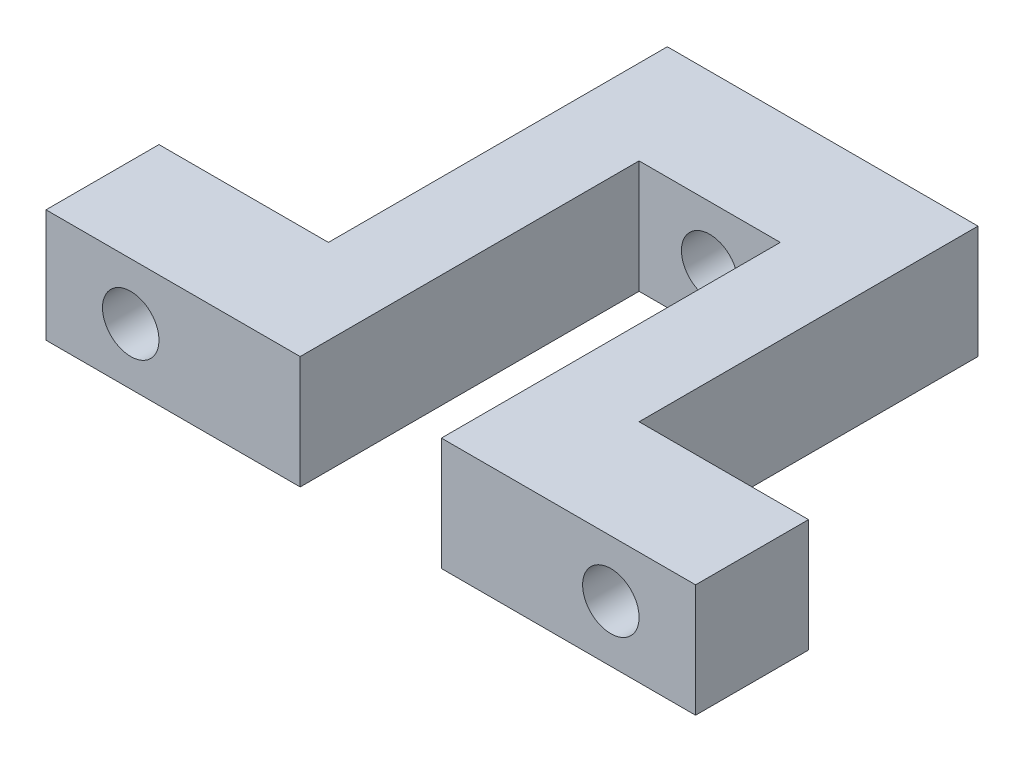
SolidWorks part; units mm, degrees
material "Copper"
ref_plane "Front Plane" through (0, 0, 0) normal (0, 0, 1) x (1, 0, 0)
ref_plane "Top Plane" through (0, 0, 0) normal (0, 1, 0) x (1, 0, 0)
ref_plane "Right Plane" through (0, 0, 0) normal (1, 0, 0) x (0, 0, -1)
sketch "Sketch1" plane through (0, 0, 0) normal (0, 1, 0) x (1, 0, 0)
  line L0 (-70, -38.8484) -> (-70, -18.8484)
  line L1 (-70, -18.8484) -> (-40, -18.8484)
  line L2 (-40, -18.8484) -> (-40, 41.1516)
  line L3 (-40, 41.1516) -> (15, 41.1516)
  line L4 (15, 41.1516) -> (15, -18.8484)
  line L5 (15, -18.8484) -> (45, -18.8484)
  line L6 (45, -18.8484) -> (45, -38.8484)
  line L7 (45, -38.8484) -> (0, -38.8484)
  line L8 (0, -38.8484) -> (0, 21.1516)
  line L9 (0, 21.1516) -> (-25, 21.1516)
  line L10 (-25, 21.1516) -> (-25, -38.8484)
  line L11 (-25, -38.8484) -> (-70, -38.8484)
  dimension "D1" = 20
  dimension "D2" = 30
  dimension "D3" = 60
  dimension "D4" = 55
  dimension "D5" = 60
  dimension "D6" = 30
  dimension "D7" = 20
  dimension "D8" = 45
  dimension "D9" = 45
  dimension "D10" = 60
extrude "Boss-Extrude1" add sketch "Sketch1" along normal blind 20
ref_plane "Plane1" through (0, 0, -41.1516) normal (0, 0, -1) x (-1, 0, 0)
sketch "Sketch2" plane through (0, 0, -41.1516) normal (0, 0, -1) x (-1, 0, 0)
  point P6 (12.5, 10)
hole_wizard "M10x1.0 Tapped Hole1" positions "3DSketch1" profile "Sketch3" tap size "M10x1.0" standard "ANSI Metric"
sketch3d "3DSketch1"
  point P0 (-12.5, 10, -41.1516)
sketch "Sketch3" plane through (-12.5, 10, -41.1516) normal (1, 0, 0) x (0, 1, 0)
  line L0 (0, 0) -> (0, 25.7039)
  line L1 (0, 25.7039) -> (4.5, 23)
  line L2 (4.5, 23) -> (4.5, 20)
  line L3 (4.5, 20) -> (5, 20)
  line L4 (5, 20) -> (5, 0)
  line L5 (5, 0) -> (0, 0)
  line L10 (0, 25.7039) -> (-4.5, 23) construction
  line L11 (0, -6.35) -> (0, 107.95) construction
  dimension "Tap Drill Dia." = 9
  dimension "Tap Drill Depth" = 23
  dimension "Thread Major Dia." = 10
  dimension "Thread Depth" = 20
  dimension "Drill Angle" = 118
ref_plane "Plane2" through (0, 0, 18.8484) normal (0, 0, -1) x (-1, 0, 0)
sketch "Sketch4" plane through (0, 0, 18.8484) normal (0, 0, -1) x (-1, 0, 0)
  point P12 (-30, 10)
  point P13 (55, 10)
hole_wizard "M10x1.0 Tapped Hole2" positions "3DSketch2" profile "Sketch5" tap size "M10x1.0" standard "ANSI Metric"
sketch3d "3DSketch2"
  point P0 (30, 10, 18.8484)
  point P3 (-55, 10, 18.8484)
sketch "Sketch5" plane through (30, 10, 18.8484) normal (1, 0, 0) x (0, 1, 0)
  line L0 (0, 0) -> (0, 25.7039)
  line L1 (0, 25.7039) -> (4.5, 23)
  line L2 (4.5, 23) -> (4.5, 20)
  line L3 (4.5, 20) -> (5, 20)
  line L4 (5, 20) -> (5, 0)
  line L5 (5, 0) -> (0, 0)
  line L10 (0, 25.7039) -> (-4.5, 23) construction
  line L11 (0, -6.35) -> (0, 107.95) construction
  dimension "Tap Drill Dia." = 9
  dimension "Tap Drill Depth" = 23
  dimension "Thread Major Dia." = 10
  dimension "Thread Depth" = 20
  dimension "Drill Angle" = 118
